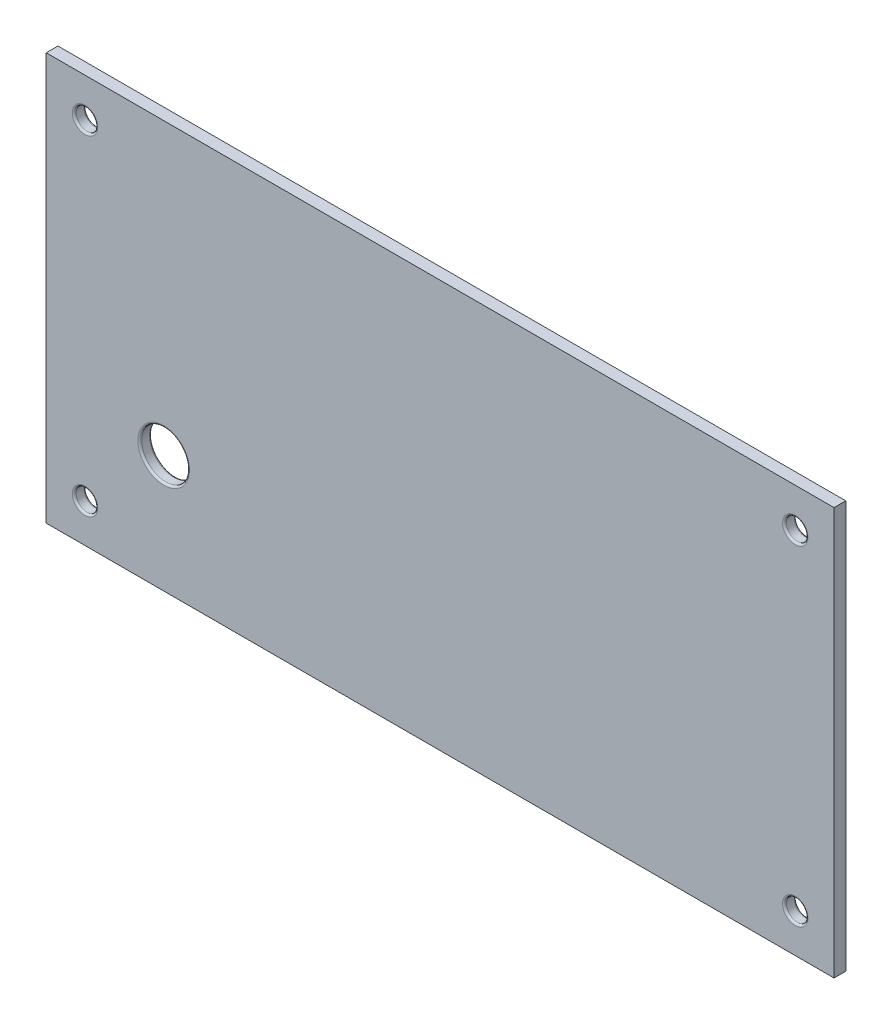
SolidWorks part; units mm, degrees
ref_plane "Front Plane" through (0, 0, 0) normal (0, 0, 1) x (1, 0, 0)
ref_plane "Top Plane" through (0, 0, 0) normal (0, 1, 0) x (1, 0, 0)
ref_plane "Right Plane" through (0, 0, 0) normal (1, 0, 0) x (0, 0, -1)
sketch "Sketch1" plane through (0, 0, 0) normal (0, 0, 1) x (1, 0, 0)
  line L1 (-100.602, -52.02) -> (100.602, -52.02)
  line L2 (-100.602, -52.02) -> (-100.602, 52.02)
  line L3 (-100.602, 52.02) -> (100.602, 52.02)
  line L4 (100.602, -52.02) -> (100.602, 52.02)
  line L5 (-100.602, -52.02) -> (100.602, 52.02) construction
  line L6 (-100.602, 52.02) -> (100.602, -52.02) construction
  point P0 (0, 0)
  dimension "D1" = 201.204
  dimension "D2" = 104.04
extrude "Boss-Extrude1" add sketch "Sketch1" along normal blind 3
sketch "Sketch2" plane through (0, 0, 3) normal (0, 0, 1) x (1, 0, 0)
  line L0 (-42.5, 0) -> (42.5, 0) construction
  line L5 (0, 0) -> (0, -50000) construction
  line L7 (-42.5, -25) -> (42.5, -25) construction
  line L8 (-42.5, -25) -> (-42.5, 25) construction
  line L9 (-42.5, 25) -> (42.5, 25) construction
  line L10 (42.5, -25) -> (42.5, 25) construction
  line L11 (-42.5, -25) -> (42.5, 25) construction
  line L12 (-42.5, 25) -> (42.5, -25) construction
  line L15 (-25.05, -15.05) -> (25.05, -15.05)
  line L16 (-25.05, -15.05) -> (-25.05, 15.05)
  line L17 (-25.05, 15.05) -> (25.05, 15.05)
  line L18 (25.05, -15.05) -> (25.05, 15.05)
  line L19 (-25.05, -15.05) -> (25.05, 15.05) construction
  line L20 (-25.05, 15.05) -> (25.05, -15.05) construction
  circle A7 centre (-35.5, 18) radius 2.75
  circle A8 centre (35.5, 18) radius 2.75
  circle A9 centre (35.5, -18) radius 2.75
  circle A10 centre (-35.5, -18) radius 2.75
  point P2 (0, 0)
  point P12 (0, 0)
  point P19 (0, 0)
  dimension "D1" = 85
  dimension "D3" = 5.5
  dimension "D2" = 50
  dimension "D4" = 7
  dimension "D5" = 7
  dimension "D6" = 50.1
  dimension "D7" = 30.1
sketch "Sketch3" plane through (0, 0, 3) normal (0, 0, 1) x (1, 0, 0)
  line L0 (-100.602, 52.02) -> (-100.602, -52.02) construction
  line L1 (100.602, 52.02) -> (-100.602, 52.02) construction
  line L2 (0, 0) -> (0, -50000) construction
  line L3 (0, 0) -> (50000, 0) construction
  circle A0 centre (-90.702, 42.12) radius 2.75
  circle A1 centre (90.702, 42.12) radius 2.75
  circle A2 centre (90.702, -42.12) radius 2.75
  circle A3 centre (-90.702, -42.12) radius 2.75
  dimension "D1" = 5.5
  dimension "D2" = 9.9
  dimension "D3" = 9.9
extrude "Cut-Extrude2" cut sketch "Sketch3" against normal through all
extrude "Cut-Extrude3" [suppressed] cut sketch "Sketch2" against normal through all
fillet "Fillet1" [suppressed] radius 0.5
fillet "Fillet2" radius 0.5 8 edges at (87.952, 42.12, 3) (87.952, 42.12, 0) (93.452, -42.12, 3) (93.452, -42.12, 0) (-93.452, -42.12, 3) (-93.452, -42.12, 0) (-87.952, 42.12, 3) (-87.952, 42.12, 0)
sketch "Sketch4" plane through (0, 0, 3) normal (0, 0, 1) x (1, 0, 0)
  line L6 (-100.602, -52.02) -> (100.602, -52.02) construction
  line L7 (0, 0) -> (0, -50000) construction
  line L8 (-100.602, 52.02) -> (-100.602, -52.02) construction
  circle A0 centre (-70.602, -22.02) radius 6.1
  dimension "D1" = 12.2
  dimension "D2" = 30
  dimension "D3" = 30
extrude "Cut-Extrude4" cut sketch "Sketch4" against normal through all
fillet "Fillet3" radius 0.5 2 edges at (-64.502, -22.02, 3) (-64.502, -22.02, 0)
